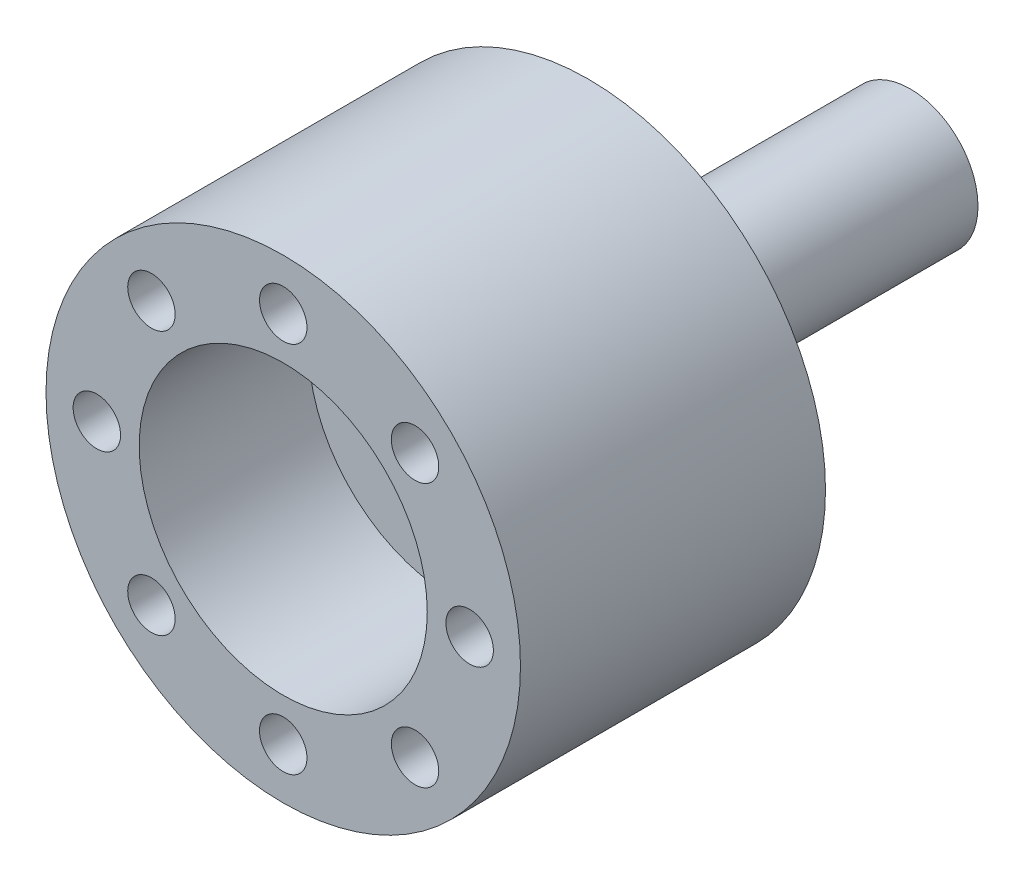
SolidWorks part; units mm, degrees
ref_plane "정면" through (0, 0, 0) normal (0, 0, 1) x (1, 0, 0)
ref_plane "윗면" through (0, 0, 0) normal (0, 1, 0) x (1, 0, 0)
ref_plane "우측면" through (0, 0, 0) normal (1, 0, 0) x (0, 0, -1)
sketch "Sketch1" plane through (0, 0, 0) normal (0, 0, 1) x (1, 0, 0)
  circle A0 centre (0, 0) radius 14
  dimension "D1" = 28
extrude "Boss-Extrude1" add sketch "Sketch1" along normal blind 18
sketch "Sketch2" plane through (0, 0, 18) normal (0, 0, 1) x (1, 0, 0)
  line L0 (0, 0) -> (4.655, 4.1705) construction
  circle A0 centre (4.655, 4.1705) radius 1.45
  dimension "D2" = 2.9
  dimension "D1" = 6.25
extrude "Cut-Extrude1" cut sketch "Sketch2" against normal blind 15
sketch "Sketch3" plane through (0, 0, 18) normal (0, 0, 1) x (1, 0, 0)
  line L0 (0, 11) -> (0, 0) construction
  circle A1 centre (0, 11) radius 1.4
  dimension "D1" = 11
  dimension "D2" = 2.8
extrude "Cut-Extrude2" cut sketch "Sketch3" against normal blind 6
sketch "Sketch4" plane through (0, 0, 0) normal (1, 0, 0) x (0, 0, -1)
  line L0 (-18, 0) -> (0, 0) construction
  line L1 (-18, 14) -> (-18, -14) construction
pattern_circular "CirPattern1" count 8 over 360 about axis through (0, 0, 0) along (0, 0, 1) of "Cut-Extrude2"
sketch "Sketch5" plane through (0, 0, 0) normal (0, 0, -1) x (-1, 0, 0)
  circle A0 centre (0, 11) radius 2.25
  dimension "D1" = 4.5
extrude "Cut-Extrude3" cut sketch "Sketch5" against normal blind 15 contours A0
pattern_circular "CirPattern2" count 8 over 360 about axis through (0, 0, 0) along (0, 0, 1) of "Cut-Extrude3"
sketch "Sketch6" plane through (0, 0, 0) normal (0, 0, -1) x (-1, 0, 0)
  circle A0 centre (0, 0) radius 4
  dimension "D1" = 8
extrude "Boss-Extrude2" add sketch "Sketch6" along normal blind 19
sketch "Sketch7" plane through (0, 0, 18) normal (0, 0, 1) x (1, 0, 0)
  circle A0 centre (0, 0) radius 8.5
  dimension "D1" = 17
extrude "Cut-Extrude4" cut sketch "Sketch7" against normal blind 10
sketch "Sketch8" plane through (0, 0, 0) normal (0, 0, -1) x (-1, 0, 0)
  circle A0 centre (0, 0) radius 7.75
  circle A1 centre (0, 0) radius 4.75
extrude "Cut-Extrude5" cut sketch "Sketch8" against normal blind 5
sketch "Sketch9" plane through (0, 0, 0) normal (0, 1, 0) x (1, 0, 0)
  line L0 (4, 1.5575) -> (4.75, 0)
  line L1 (4, 0) -> (4, 19) construction
  line L2 (4.75, 0) -> (4, 0)
  line L3 (4, 0) -> (-4, 0) construction
  line L4 (14, 0) -> (-14, 0) construction
  line L5 (4, 0) -> (4, 1.5575)
revolve "Revolve1" add sketch "Sketch9" angle 360 about L0
sketch "Sketch10" plane through (0, 0, -19) normal (0, 0, -1) x (-1, 0, 0)
  circle A0 centre (0, 0) radius 3.25
  dimension "D1" = 6.5
extrude "Cut-Extrude6" cut sketch "Sketch10" against normal blind 2.5
